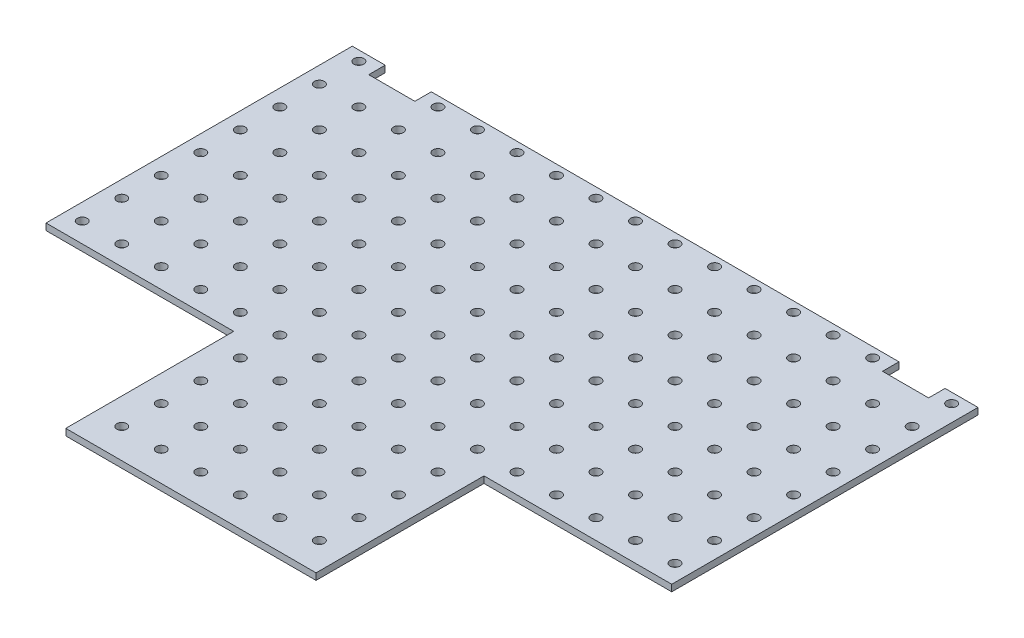
SolidWorks part; units mm, degrees
ref_plane "Front Plane" through (0, 0, 0) normal (0, 0, 1) x (1, 0, 0)
ref_plane "Top Plane" through (0, 0, 0) normal (0, 1, 0) x (1, 0, 0)
ref_plane "Right Plane" through (0, 0, 0) normal (1, 0, 0) x (0, 0, -1)
sketch "Sketch1" plane through (0, 0, 0) normal (0, 1, 0) x (1, 0, 0)
  line L0 (-100, -24) -> (-43, -24)
  line L2 (-100, 69) -> (-100, -24)
  line L3 (-43, -75) -> (33, -75)
  line L4 (90, 69) -> (90, -24)
  line L5 (-5, 69) -> (-5, -75) construction
  line L6 (33, -24) -> (33, -75)
  line L7 (-43, -24) -> (-43, -75)
  line L8 (-100, 69) -> (90, 69)
  line L10 (90, -24) -> (33, -24)
  circle A0 centre (-95, 66) radius 1.5
  circle A156 centre (-83, 66) radius 1.5
  circle A157 centre (-71, 66) radius 1.5
  circle A158 centre (-59, 66) radius 1.5
  circle A159 centre (-47, 66) radius 1.5
  circle A160 centre (-35, 66) radius 1.5
  circle A161 centre (-23, 66) radius 1.5
  circle A162 centre (-11, 66) radius 1.5
  circle A163 centre (1, 66) radius 1.5
  circle A164 centre (13, 66) radius 1.5
  circle A165 centre (25, 66) radius 1.5
  circle A166 centre (37, 66) radius 1.5
  circle A167 centre (49, 66) radius 1.5
  circle A168 centre (61, 66) radius 1.5
  circle A169 centre (73, 66) radius 1.5
  circle A170 centre (85, 66) radius 1.5
  circle A171 centre (-83, 54) radius 1.5
  circle A172 centre (-71, 54) radius 1.5
  circle A173 centre (-59, 54) radius 1.5
  circle A174 centre (-47, 54) radius 1.5
  circle A175 centre (-35, 54) radius 1.5
  circle A176 centre (-23, 54) radius 1.5
  circle A177 centre (-11, 54) radius 1.5
  circle A178 centre (1, 54) radius 1.5
  circle A179 centre (13, 54) radius 1.5
  circle A180 centre (25, 54) radius 1.5
  circle A181 centre (37, 54) radius 1.5
  circle A182 centre (49, 54) radius 1.5
  circle A183 centre (61, 54) radius 1.5
  circle A184 centre (73, 54) radius 1.5
  circle A185 centre (85, 54) radius 1.5
  circle A186 centre (-83, 42) radius 1.5
  circle A187 centre (-71, 42) radius 1.5
  circle A188 centre (-59, 42) radius 1.5
  circle A189 centre (-47, 42) radius 1.5
  circle A190 centre (-35, 42) radius 1.5
  circle A191 centre (-23, 42) radius 1.5
  circle A192 centre (-11, 42) radius 1.5
  circle A193 centre (1, 42) radius 1.5
  circle A194 centre (13, 42) radius 1.5
  circle A195 centre (25, 42) radius 1.5
  circle A196 centre (37, 42) radius 1.5
  circle A197 centre (49, 42) radius 1.5
  circle A198 centre (61, 42) radius 1.5
  circle A199 centre (73, 42) radius 1.5
  circle A200 centre (85, 42) radius 1.5
  circle A201 centre (-83, 30) radius 1.5
  circle A202 centre (-71, 30) radius 1.5
  circle A203 centre (-59, 30) radius 1.5
  circle A204 centre (-47, 30) radius 1.5
  circle A205 centre (-35, 30) radius 1.5
  circle A206 centre (-23, 30) radius 1.5
  circle A207 centre (-11, 30) radius 1.5
  circle A208 centre (1, 30) radius 1.5
  circle A209 centre (13, 30) radius 1.5
  circle A210 centre (25, 30) radius 1.5
  circle A211 centre (37, 30) radius 1.5
  circle A212 centre (49, 30) radius 1.5
  circle A213 centre (61, 30) radius 1.5
  circle A214 centre (73, 30) radius 1.5
  circle A215 centre (85, 30) radius 1.5
  circle A216 centre (-83, 18) radius 1.5
  circle A217 centre (-71, 18) radius 1.5
  circle A218 centre (-59, 18) radius 1.5
  circle A219 centre (-47, 18) radius 1.5
  circle A220 centre (-35, 18) radius 1.5
  circle A221 centre (-23, 18) radius 1.5
  circle A222 centre (-11, 18) radius 1.5
  circle A223 centre (1, 18) radius 1.5
  circle A224 centre (13, 18) radius 1.5
  circle A225 centre (25, 18) radius 1.5
  circle A226 centre (37, 18) radius 1.5
  circle A227 centre (49, 18) radius 1.5
  circle A228 centre (61, 18) radius 1.5
  circle A229 centre (73, 18) radius 1.5
  circle A230 centre (85, 18) radius 1.5
  circle A231 centre (-83, 6) radius 1.5
  circle A232 centre (-71, 6) radius 1.5
  circle A233 centre (-59, 6) radius 1.5
  circle A234 centre (-47, 6) radius 1.5
  circle A235 centre (-35, 6) radius 1.5
  circle A236 centre (-23, 6) radius 1.5
  circle A237 centre (-11, 6) radius 1.5
  circle A238 centre (1, 6) radius 1.5
  circle A239 centre (13, 6) radius 1.5
  circle A240 centre (25, 6) radius 1.5
  circle A241 centre (37, 6) radius 1.5
  circle A242 centre (49, 6) radius 1.5
  circle A243 centre (61, 6) radius 1.5
  circle A244 centre (73, 6) radius 1.5
  circle A245 centre (85, 6) radius 1.5
  circle A246 centre (-83, -6) radius 1.5
  circle A247 centre (-71, -6) radius 1.5
  circle A248 centre (-59, -6) radius 1.5
  circle A249 centre (-47, -6) radius 1.5
  circle A250 centre (-35, -6) radius 1.5
  circle A251 centre (-23, -6) radius 1.5
  circle A252 centre (-11, -6) radius 1.5
  circle A253 centre (1, -6) radius 1.5
  circle A254 centre (13, -6) radius 1.5
  circle A255 centre (25, -6) radius 1.5
  circle A256 centre (37, -6) radius 1.5
  circle A257 centre (49, -6) radius 1.5
  circle A258 centre (61, -6) radius 1.5
  circle A259 centre (73, -6) radius 1.5
  circle A260 centre (85, -6) radius 1.5
  circle A261 centre (-83, -18) radius 1.5
  circle A262 centre (-71, -18) radius 1.5
  circle A263 centre (-59, -18) radius 1.5
  circle A264 centre (-47, -18) radius 1.5
  circle A265 centre (-35, -18) radius 1.5
  circle A266 centre (-23, -18) radius 1.5
  circle A267 centre (-11, -18) radius 1.5
  circle A268 centre (1, -18) radius 1.5
  circle A269 centre (13, -18) radius 1.5
  circle A270 centre (25, -18) radius 1.5
  circle A271 centre (37, -18) radius 1.5
  circle A272 centre (49, -18) radius 1.5
  circle A273 centre (61, -18) radius 1.5
  circle A274 centre (73, -18) radius 1.5
  circle A275 centre (85, -18) radius 1.5
  circle A280 centre (-35, -30) radius 1.5
  circle A281 centre (-23, -30) radius 1.5
  circle A282 centre (-11, -30) radius 1.5
  circle A283 centre (1, -30) radius 1.5
  circle A284 centre (13, -30) radius 1.5
  circle A285 centre (25, -30) radius 1.5
  circle A295 centre (-35, -42) radius 1.5
  circle A296 centre (-23, -42) radius 1.5
  circle A297 centre (-11, -42) radius 1.5
  circle A298 centre (1, -42) radius 1.5
  circle A299 centre (13, -42) radius 1.5
  circle A300 centre (25, -42) radius 1.5
  circle A310 centre (-35, -54) radius 1.5
  circle A311 centre (-23, -54) radius 1.5
  circle A312 centre (-11, -54) radius 1.5
  circle A313 centre (1, -54) radius 1.5
  circle A314 centre (13, -54) radius 1.5
  circle A315 centre (25, -54) radius 1.5
  circle A325 centre (-35, -66) radius 1.5
  circle A326 centre (-23, -66) radius 1.5
  circle A327 centre (-11, -66) radius 1.5
  circle A328 centre (1, -66) radius 1.5
  circle A329 centre (13, -66) radius 1.5
  circle A330 centre (25, -66) radius 1.5
  circle A336 centre (-95, 54) radius 1.5
  circle A337 centre (-95, 42) radius 1.5
  circle A338 centre (-95, 30) radius 1.5
  circle A339 centre (-95, 18) radius 1.5
  circle A340 centre (-95, 6) radius 1.5
  circle A341 centre (-95, -6) radius 1.5
  circle A342 centre (-95, -18) radius 1.5
  circle A347 centre (-83, -30) radius 1.5 [skipped]
  circle A348 centre (-71, -30) radius 1.5 [skipped]
  circle A349 centre (-59, -30) radius 1.5 [skipped]
  circle A350 centre (-47, -30) radius 1.5 [skipped]
  circle A351 centre (-83, -42) radius 1.5 [skipped]
  circle A352 centre (-71, -42) radius 1.5 [skipped]
  circle A353 centre (-59, -42) radius 1.5 [skipped]
  circle A354 centre (-47, -42) radius 1.5 [skipped]
  circle A355 centre (-83, -54) radius 1.5 [skipped]
  circle A356 centre (-71, -54) radius 1.5 [skipped]
  circle A357 centre (-59, -54) radius 1.5 [skipped]
  circle A358 centre (-47, -54) radius 1.5 [skipped]
  circle A359 centre (-83, -66) radius 1.5 [skipped]
  circle A360 centre (-71, -66) radius 1.5 [skipped]
  circle A361 centre (-59, -66) radius 1.5 [skipped]
  circle A362 centre (-47, -66) radius 1.5 [skipped]
  circle A363 centre (-95, -30) radius 1.5 [skipped]
  circle A364 centre (-95, -42) radius 1.5 [skipped]
  circle A365 centre (-95, -54) radius 1.5 [skipped]
  circle A366 centre (-95, -66) radius 1.5 [skipped]
  circle A367 centre (85, -66) radius 1.5 [skipped]
  circle A368 centre (85, -54) radius 1.5 [skipped]
  circle A369 centre (85, -42) radius 1.5 [skipped]
  circle A370 centre (85, -30) radius 1.5 [skipped]
  circle A371 centre (37, -30) radius 1.5 [skipped]
  circle A372 centre (49, -30) radius 1.5 [skipped]
  circle A373 centre (61, -30) radius 1.5 [skipped]
  circle A374 centre (73, -30) radius 1.5 [skipped]
  circle A375 centre (37, -42) radius 1.5 [skipped]
  circle A376 centre (49, -42) radius 1.5 [skipped]
  circle A377 centre (61, -42) radius 1.5 [skipped]
  circle A378 centre (73, -42) radius 1.5 [skipped]
  circle A379 centre (37, -54) radius 1.5 [skipped]
  circle A380 centre (49, -54) radius 1.5 [skipped]
  circle A381 centre (61, -54) radius 1.5 [skipped]
  circle A382 centre (73, -54) radius 1.5 [skipped]
  circle A383 centre (37, -66) radius 1.5 [skipped]
  circle A384 centre (49, -66) radius 1.5 [skipped]
  circle A385 centre (61, -66) radius 1.5 [skipped]
  circle A386 centre (73, -66) radius 1.5 [skipped]
  dimension "D3" = 3
  dimension "D4" = 144
  dimension "D5" = 5
  dimension "D8" = 100
  dimension "D9" = 75
  dimension "D10" = 1
  dimension "D12" = 57
  dimension "D7" = 3
  dimension "D2" = 16
  dimension "D11" = 6
  dimension "D13" = 6
  dimension "D15" = 190
  dimension "D6" = 12
extrude "Boss-Extrude1" add sketch "Sketch1" along normal blind 2
sketch "Sketch2" plane through (0, 2, 0) normal (0, 1, 0) x (1, 0, 0)
  line L0 (90, 69) -> (-100, 69) construction
  line L1 (-90, 69) -> (-76, 69)
  line L2 (-90, 69) -> (-90, 64)
  line L3 (-90, 64) -> (-76, 64)
  line L4 (-76, 69) -> (-76, 64)
  line L5 (-100, 69) -> (-100, -24) construction
  line L6 (-5, 69) -> (-5, 10.0116) construction
  line L7 (80, 64) -> (66, 64)
  line L8 (66, 69) -> (66, 64)
  line L9 (80, 69) -> (66, 69)
  line L10 (80, 69) -> (80, 64)
  dimension "D1" = 10
  dimension "D2" = 5
  dimension "D3" = 14
extrude "Cut-Extrude1" cut sketch "Sketch2" against normal blind 10
